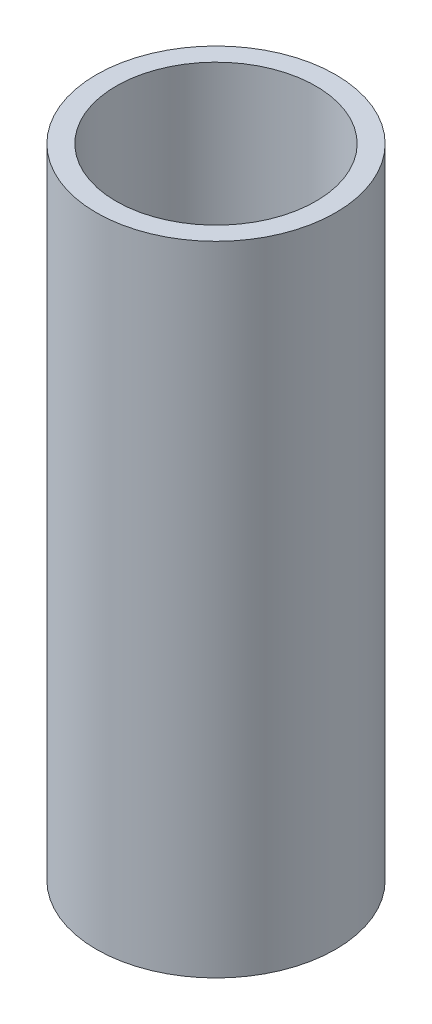
SolidWorks part; units mm, degrees
ref_plane "Front Plane" through (0, 0, 0) normal (0, 0, 1) x (1, 0, 0)
ref_plane "Top Plane" through (0, 0, 0) normal (0, 1, 0) x (1, 0, 0)
ref_plane "Right Plane" through (0, 0, 0) normal (1, 0, 0) x (0, 0, -1)
sketch "Sketch1" plane through (0, 0, 0) normal (0, 1, 0) x (1, 0, 0)
  circle A0 centre (0, 0) radius 9.525
  circle A1 centre (0, 0) radius 7.9502
extrude "Boss-Extrude1" add sketch "Sketch1" along normal blind 50.8
